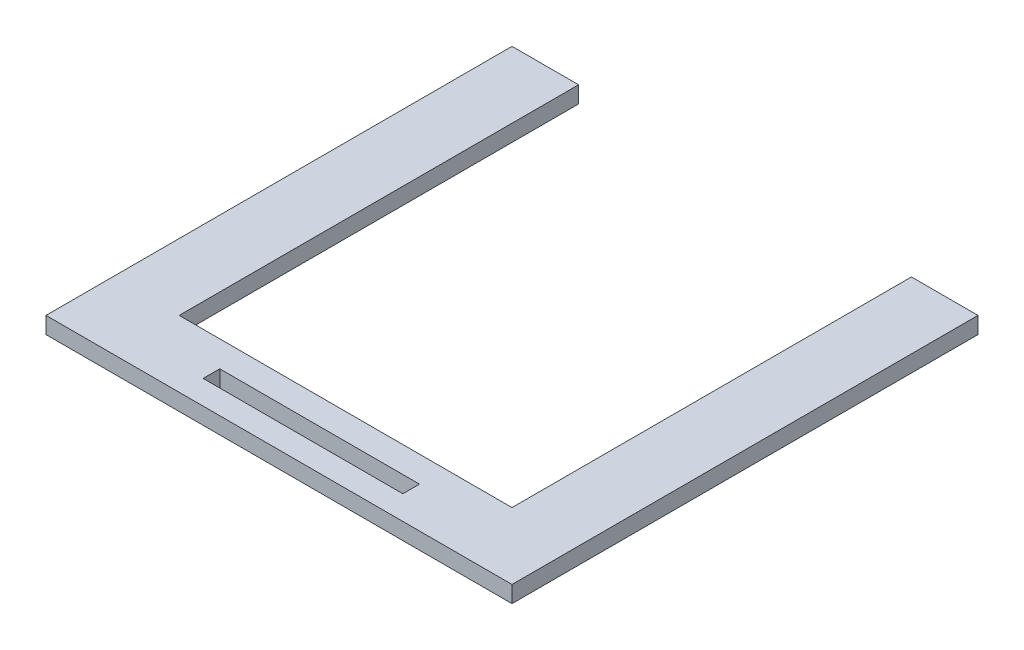
SolidWorks part; units mm, degrees
ref_plane "Front Plane" through (0, 0, 0) normal (0, 0, 1) x (1, 0, 0)
ref_plane "Top Plane" through (0, 0, 0) normal (0, 1, 0) x (1, 0, 0)
ref_plane "Right Plane" through (0, 0, 0) normal (1, 0, 0) x (0, 0, -1)
sketch "Sketch2" plane through (0, 0, 0) normal (0, 1, 0) x (1, 0, 0)
  line L0 (-44.1998, 37.8875) -> (-31.4998, 37.8875)
  line L1 (32.0002, 37.8875) -> (44.7002, 37.8875)
  line L2 (32.0002, 37.8875) -> (32.0002, -38.3125)
  line L4 (44.7002, 37.8875) -> (44.7002, -38.3125)
  line L5 (-44.1998, 37.8875) -> (-44.1998, -38.3125)
  line L7 (-31.4998, 37.8875) -> (-31.4998, -38.3125)
  line L9 (-31.4998, -38.3125) -> (32.0002, -38.3125)
  line L10 (-44.1998, -38.3125) -> (-44.1998, -51.0125)
  line L11 (-44.1998, -51.0125) -> (44.7002, -51.0125)
  line L12 (44.7002, -38.3125) -> (44.7002, -51.0125)
  dimension "D1" = 76.2
  dimension "D2" = 12.7
  dimension "D4" = 12.7
  dimension "D5" = 88.9
extrude "Boss-Extrude1" add sketch "Sketch2" along normal blind 3.175
sketch "Sketch3" plane through (0, 3.175, 0) normal (0, 1, 0) x (1, 0, 0)
  line L0 (-31.4998, -38.3125) -> (-31.4998, 37.8875) construction
  line L1 (-18.7998, -43.2655) -> (19.3002, -43.2655)
  line L2 (-18.7998, -43.2655) -> (-18.7998, -46.4405)
  line L3 (-18.7998, -46.4405) -> (19.3002, -46.4405)
  line L4 (19.3002, -43.2655) -> (19.3002, -46.4405)
  line L5 (32.0002, 37.8875) -> (32.0002, -38.3125) construction
  dimension "D1" = 12.7
  dimension "D2" = 12.7
  dimension "D3" = 3.175
extrude "Cut-Extrude1" cut sketch "Sketch3" against normal blind 3.175
